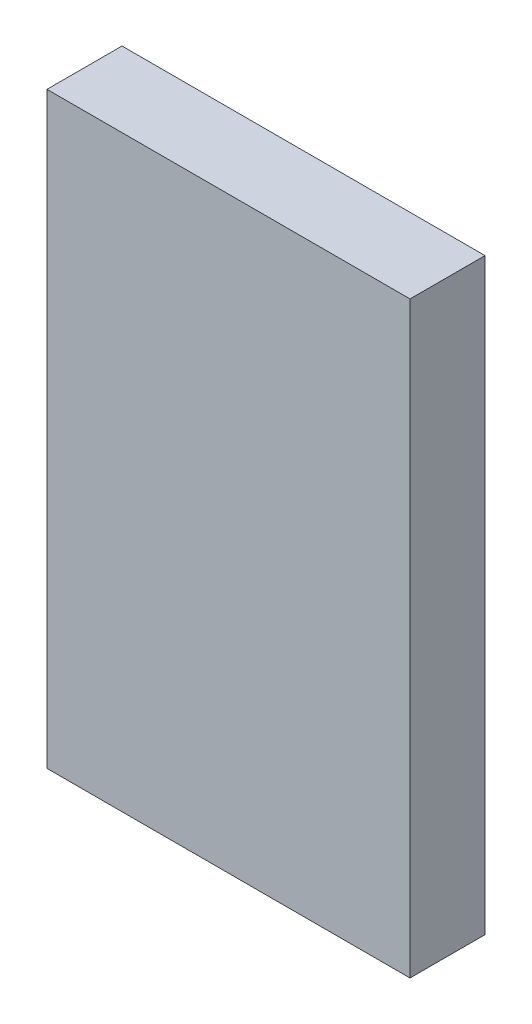
SolidWorks part; units mm, degrees
ref_plane "Front Plane" through (0, 0, 0) normal (0, 0, 1) x (1, 0, 0)
ref_plane "Top Plane" through (0, 0, 0) normal (0, 1, 0) x (1, 0, 0)
ref_plane "Right Plane" through (0, 0, 0) normal (1, 0, 0) x (0, 0, -1)
sketch "Sketch2" plane through (0, 0, 0) normal (0, 1, 0) x (1, 0, 0)
  line L1 (19.05, -3.937) -> (-19.05, -3.937)
  line L2 (19.05, -3.937) -> (19.05, 3.937)
  line L3 (19.05, 3.937) -> (-19.05, 3.937)
  line L4 (-19.05, -3.937) -> (-19.05, 3.937)
  line L5 (19.05, -3.937) -> (-19.05, 3.937) construction
  line L6 (19.05, 3.937) -> (-19.05, -3.937) construction
  point P0 (0, 0)
  dimension "D1" = 7.874
  dimension "D2" = 38.1
extrude "Boss-Extrude1" add sketch "Sketch2" along normal blind 61.722
